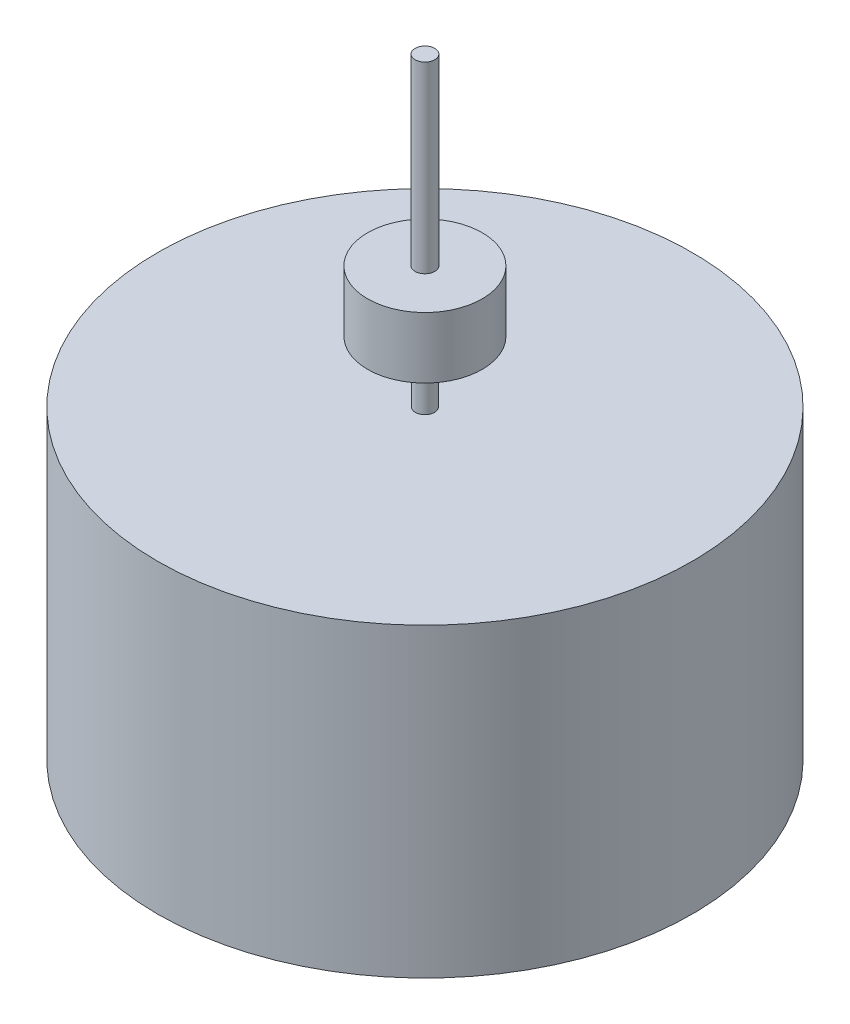
SolidWorks part; units mm, degrees
material "ASTM A36 Steel"
ref_plane "Front Plane" through (0, 0, 0) normal (0, 0, 1) x (1, 0, 0)
ref_plane "Top Plane" through (0, 0, 0) normal (0, 1, 0) x (1, 0, 0)
ref_plane "Right Plane" through (0, 0, 0) normal (1, 0, 0) x (0, 0, -1)
sketch "Sketch1" plane through (0, 0, 0) normal (0, 1, 0) x (1, 0, 0)
  circle A0 centre (0, 0) radius 11.1125
  dimension "D1" = 22.225
extrude "Boss-Extrude1" add sketch "Sketch1" along normal blind 12.7
sketch "Sketch2" plane through (0, 12.7, 0) normal (0, 1, 0) x (1, 0, 0)
  circle A0 centre (0, 0) radius 0.3969
  dimension "D1" = 0.7937
extrude "Boss-Extrude2" add sketch "Sketch2" along normal blind 2.54
sketch "Sketch3" plane through (0, 15.24, 0) normal (0, 1, 0) x (1, 0, 0)
  circle A0 centre (0, 0) radius 2.3813
  dimension "D1" = 4.7625
extrude "Boss-Extrude3" add sketch "Sketch3" along normal blind 2.54
sketch "Sketch4" plane through (0, 17.78, 0) normal (0, 1, 0) x (1, 0, 0)
  circle A0 centre (0, 0) radius 0.4097
  dimension "D1" = 0.8194
extrude "Boss-Extrude4" add sketch "Sketch4" along normal blind 7.62
